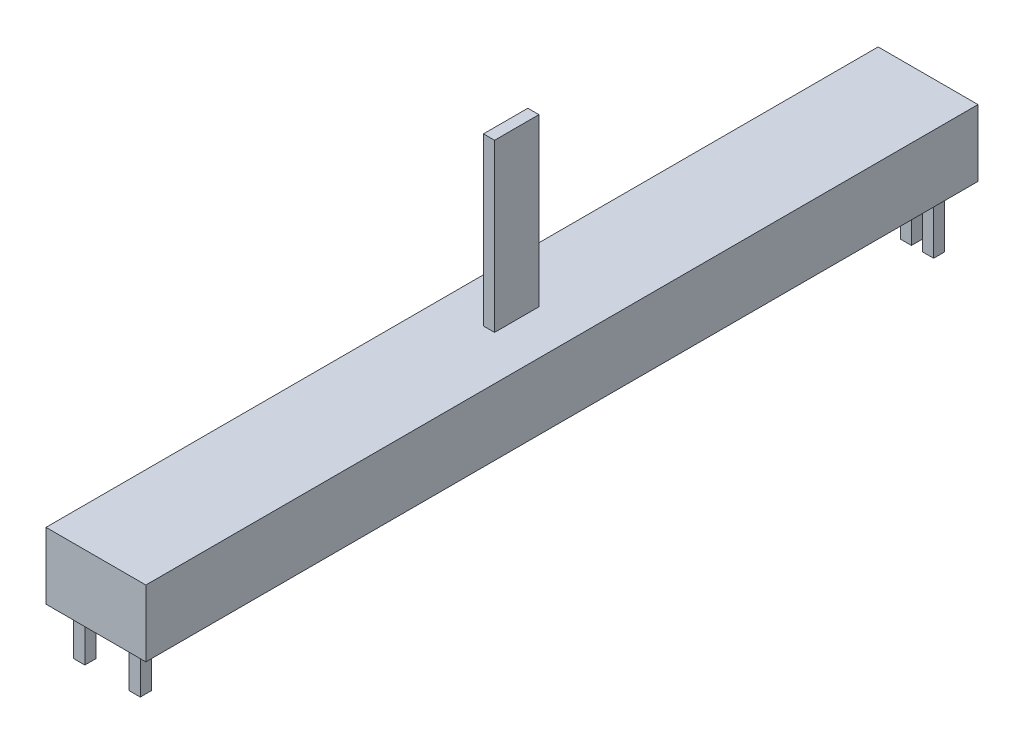
SolidWorks part; units mm, degrees
ref_plane "Front Plane" through (0, 0, 0) normal (0, 0, 1) x (1, 0, 0)
ref_plane "Top Plane" through (0, 0, 0) normal (0, 1, 0) x (1, 0, 0)
ref_plane "Right Plane" through (0, 0, 0) normal (1, 0, 0) x (0, 0, -1)
sketch "Sketch1" plane through (0, 0, 0) normal (0, 1, 0) x (1, 0, 0)
  line L1 (-4.5, -37.5) -> (4.5, -37.5)
  line L2 (-4.5, -37.5) -> (-4.5, 37.5)
  line L3 (-4.5, 37.5) -> (4.5, 37.5)
  line L4 (4.5, -37.5) -> (4.5, 37.5)
  line L5 (-4.5, -37.5) -> (4.5, 37.5) construction
  line L6 (-4.5, 37.5) -> (4.5, -37.5) construction
  point P0 (0, 0)
  dimension "D1" = 75
  dimension "D2" = 9
extrude "Boss-Extrude1" add sketch "Sketch1" along normal blind 6
sketch "Sketch2" plane through (0, 6, 0) normal (0, 1, 0) x (1, 0, 0)
  line L0 (0, 37.5) -> (0, -37.5) construction
  line L1 (4.5, 37.5) -> (-4.5, 37.5) construction
  line L2 (-4.5, -37.5) -> (4.5, -37.5) construction
  line L3 (-0.5, -2.0717) -> (0.5, -2.0717)
  line L4 (0.5, -2.0717) -> (0.5, 1.9283)
  line L5 (-0.5, -2.0717) -> (-0.5, 1.9283)
  line L6 (-0.5, 1.9283) -> (0.5, 1.9283)
  dimension "D1" = 1
  dimension "D2" = 4
extrude "Boss-Extrude2" add sketch "Sketch2" along normal blind 15
sketch "Sketch4" plane through (0, 0, 0) normal (0, -1, 0) x (1, 0, 0)
  line L0 (-4.5, 37.5) -> (4.5, 37.5) construction
  line L1 (-4, 35.5) -> (-3, 35.5)
  line L2 (-4, 35.5) -> (-4, 34.5)
  line L3 (-4, 34.5) -> (-3, 34.5)
  line L4 (-3, 35.5) -> (-3, 34.5)
  line L5 (1, 35.5) -> (2, 35.5)
  line L6 (1, 35.5) -> (1, 34.5)
  line L7 (1, 34.5) -> (2, 34.5)
  line L8 (2, 35.5) -> (2, 34.5)
  line L9 (-4.5, -37.5) -> (-4.5, 37.5) construction
  line L10 (-4.5, -35.5) -> (4.5, -35.5) construction
  line L11 (4.5, 37.5) -> (4.5, -37.5) construction
  line L12 (4.5, -37.5) -> (-4.5, -37.5) construction
  line L14 (-3.5, -35.5) -> (-2.5, -35.5)
  line L15 (-3.5, -35.5) -> (-3.5, -34.5)
  line L16 (-3.5, -34.5) -> (-2.5, -34.5)
  line L17 (-2.5, -35.5) -> (-2.5, -34.5)
  line L18 (-1.5, -35.5) -> (-0.5, -35.5)
  line L19 (-1.5, -35.5) -> (-1.5, -34.5)
  line L20 (-1.5, -34.5) -> (-0.5, -34.5)
  line L21 (-0.5, -35.5) -> (-0.5, -34.5)
  line L22 (0.5, -35.5) -> (1.5, -35.5)
  line L23 (0.5, -35.5) -> (0.5, -34.5)
  line L24 (0.5, -34.5) -> (1.5, -34.5)
  line L25 (1.5, -35.5) -> (1.5, -34.5)
  line L26 (2.5, -35.5) -> (3.5, -35.5)
  line L27 (2.5, -35.5) -> (2.5, -34.5)
  line L28 (2.5, -34.5) -> (3.5, -34.5)
  line L29 (3.5, -35.5) -> (3.5, -34.5)
  point P34 (0.5, -35)
  dimension "D1" = 1
  dimension "D2" = 2
  dimension "D3" = 1
  dimension "D4" = 1
  dimension "D5" = 0.5
  dimension "D6" = 2
  dimension "D7" = 1
  dimension "D8" = 4
  dimension "D9" = 2
  dimension "D10" = 1
  dimension "D11" = 1
  dimension "D12" = 1
  dimension "D13" = 1
  dimension "D14" = 1
  dimension "D15" = 1
  dimension "D16" = 1
  dimension "D17" = 1
  dimension "D18" = 1
  dimension "D19" = 1
  dimension "D20" = 1
  dimension "D21" = 1
  dimension "D22" = 1
extrude "Boss-Extrude3" add sketch "Sketch4" along normal blind 5
